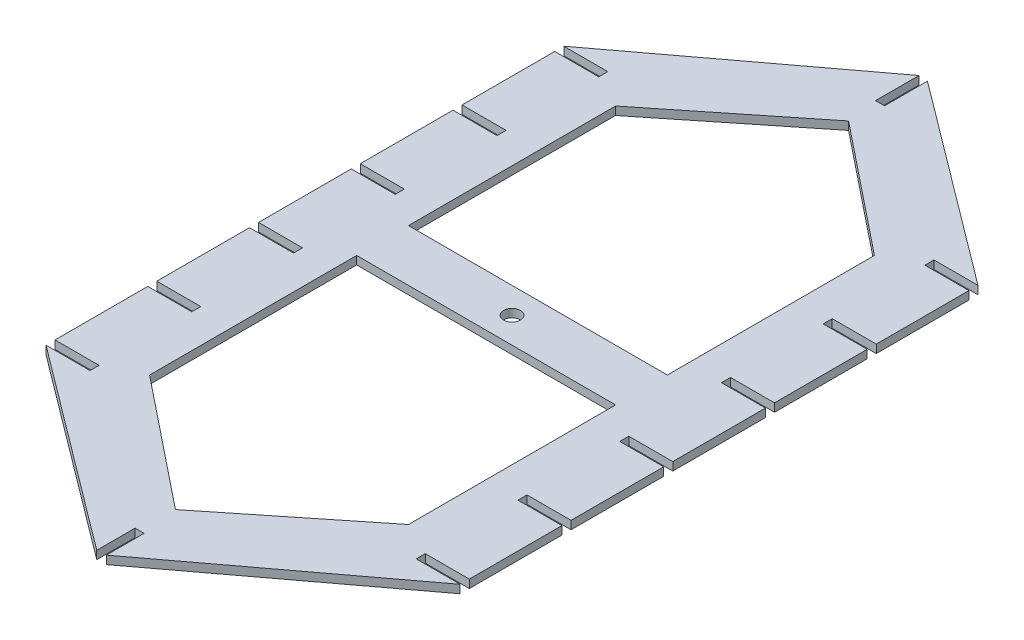
SolidWorks part; units mm, degrees
ref_plane "Front Plane" through (0, 0, 0) normal (0, 0, 1) x (1, 0, 0)
ref_plane "Top Plane" through (0, 0, 0) normal (0, 1, 0) x (1, 0, 0)
ref_plane "Right Plane" through (0, 0, 0) normal (1, 0, 0) x (0, 0, -1)
sketch "Sketch2" plane through (0, 0, 0) normal (0, 1, 0) x (1, 0, 0)
  line L0 (0, 200) -> (80, 260)
  line L2 (0, 0) -> (0, 200)
  line L4 (160, 0) -> (160, 200)
  line L5 (80, 260) -> (160, 200)
  line L6 (0, 0) -> (80, -60)
  line L7 (80, -60) -> (160, 0)
  dimension "D1" = 200
  dimension "D2" = 160
  dimension "D3" = 60
  dimension "D4" = 80
  dimension "D5" = 60
  dimension "D6" = 80
extrude "Boss-Extrude1" add sketch "Sketch2" along normal blind 3.175
sketch "Sketch3" plane through (0, 3.175, 0) normal (0, 1, 0) x (1, 0, 0)
  line L0 (30, 190) -> (80, 230)
  line L1 (30, 110) -> (130, 110)
  line L2 (30, 110) -> (30, 190)
  line L4 (130, 110) -> (130, 190)
  line L5 (80, 230) -> (130, 190)
  line L6 (0, 160.7) -> (0, 157.2)
  line L7 (0, 160.7) -> (17, 160.7)
  line L8 (17, 160.7) -> (17, 157.2)
  line L9 (30, 90) -> (30, 10)
  line L10 (30, 90) -> (130, 90)
  line L11 (130, 90) -> (130, 10)
  line L12 (80, -30) -> (130, 10)
  line L13 (30, 10) -> (80, -30)
  line L14 (0, 200) -> (17, 200)
  line L15 (0, 200) -> (0, 196.5)
  line L16 (0, 196.5) -> (17, 196.5)
  line L17 (17, 200) -> (17, 196.5)
  line L18 (0, 157.2) -> (17, 157.2)
  line L19 (0, 121.4) -> (0, 117.9)
  line L20 (0, 121.4) -> (17, 121.4)
  line L21 (17, 121.4) -> (17, 117.9)
  line L22 (0, 117.9) -> (17, 117.9)
  line L23 (0, 82.1) -> (0, 78.6)
  line L24 (0, 82.1) -> (17, 82.1)
  line L25 (17, 82.1) -> (17, 78.6)
  line L26 (0, 78.6) -> (17, 78.6)
  line L27 (0, 42.8) -> (0, 39.3)
  line L28 (0, 42.8) -> (17, 42.8)
  line L29 (17, 42.8) -> (17, 39.3)
  line L30 (0, 39.3) -> (17, 39.3)
  line L31 (0, 3.5) -> (0, 0)
  line L32 (0, 3.5) -> (17, 3.5)
  line L33 (17, 3.5) -> (17, 0)
  line L34 (0, 0) -> (17, 0)
  line L36 (160, 3.5) -> (143, 3.5)
  line L37 (143, 3.5) -> (143, 0)
  line L38 (160, 0) -> (143, 0)
  line L39 (160, 3.5) -> (160, 0)
  line L40 (160, 42.8) -> (143, 42.8)
  line L41 (143, 42.8) -> (143, 39.3)
  line L42 (160, 39.3) -> (143, 39.3)
  line L43 (160, 42.8) -> (160, 39.3)
  line L44 (160, 82.1) -> (143, 82.1)
  line L45 (143, 82.1) -> (143, 78.6)
  line L46 (160, 78.6) -> (143, 78.6)
  line L47 (160, 82.1) -> (160, 78.6)
  line L48 (160, 121.4) -> (143, 121.4)
  line L49 (143, 121.4) -> (143, 117.9)
  line L50 (160, 117.9) -> (143, 117.9)
  line L51 (160, 121.4) -> (160, 117.9)
  line L52 (160, 160.7) -> (143, 160.7)
  line L53 (143, 160.7) -> (143, 157.2)
  line L54 (160, 157.2) -> (143, 157.2)
  line L55 (160, 160.7) -> (160, 157.2)
  line L56 (160, 196.5) -> (143, 196.5)
  line L57 (143, 200) -> (143, 196.5)
  line L58 (160, 200) -> (143, 200)
  line L59 (160, 200) -> (160, 196.5)
  circle A0 centre (80, 100) radius 3.25
  dimension "D8" = 6.5
  dimension "D1" = 100
  dimension "D2" = 80
  dimension "D3" = 50
  dimension "D4" = 30
  dimension "D5" = 17
  dimension "D6" = 3.5
  dimension "D7" = 6
extrude "Cut-Extrude1" cut sketch "Sketch3" against normal through all
sketch "Sketch4" plane through (0, 3.175, 0) normal (0, 1, 0) x (1, 0, 0)
  line L1 (78.41, 242) -> (81.91, 242)
  line L2 (78.41, 242) -> (78.41, 260)
  line L3 (78.41, 260) -> (81.91, 260)
  line L4 (81.91, 242) -> (81.91, 260)
  line L7 (78.41, -60) -> (81.91, -60)
  line L8 (81.91, -44) -> (81.91, -60)
  line L9 (78.41, -44) -> (81.91, -44)
  line L10 (78.41, -44) -> (78.41, -60)
  dimension "D1" = 3.5
  dimension "D2" = 18
  dimension "D3" = 16
extrude "Cut-Extrude2" cut sketch "Sketch4" against normal through all
